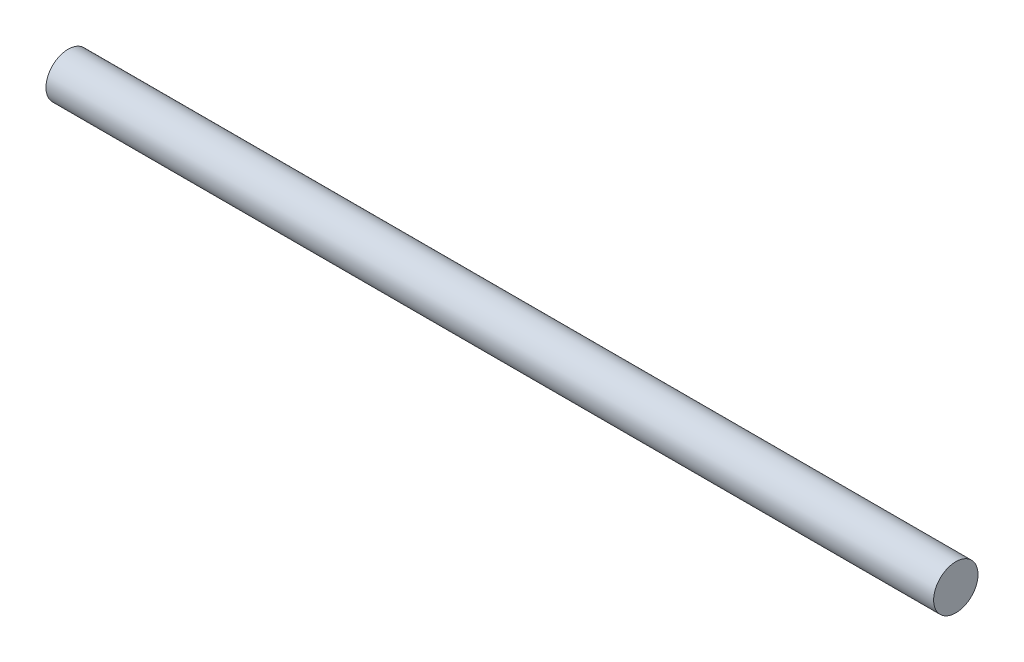
SolidWorks part; units mm, degrees
ref_plane "Front Plane" through (0, 0, 0) normal (0, 0, 1) x (1, 0, 0)
ref_plane "Top Plane" through (0, 0, 0) normal (0, 1, 0) x (1, 0, 0)
ref_plane "Right Plane" through (0, 0, 0) normal (1, 0, 0) x (0, 0, -1)
sketch "Sketch1" plane through (0, 0, 0) normal (1, 0, 0) x (0, 0, -1)
  circle A0 centre (0, 0) radius 1
  dimension "D1" = 2
extrude "Boss-Extrude1" add sketch "Sketch1" along normal blind 40
